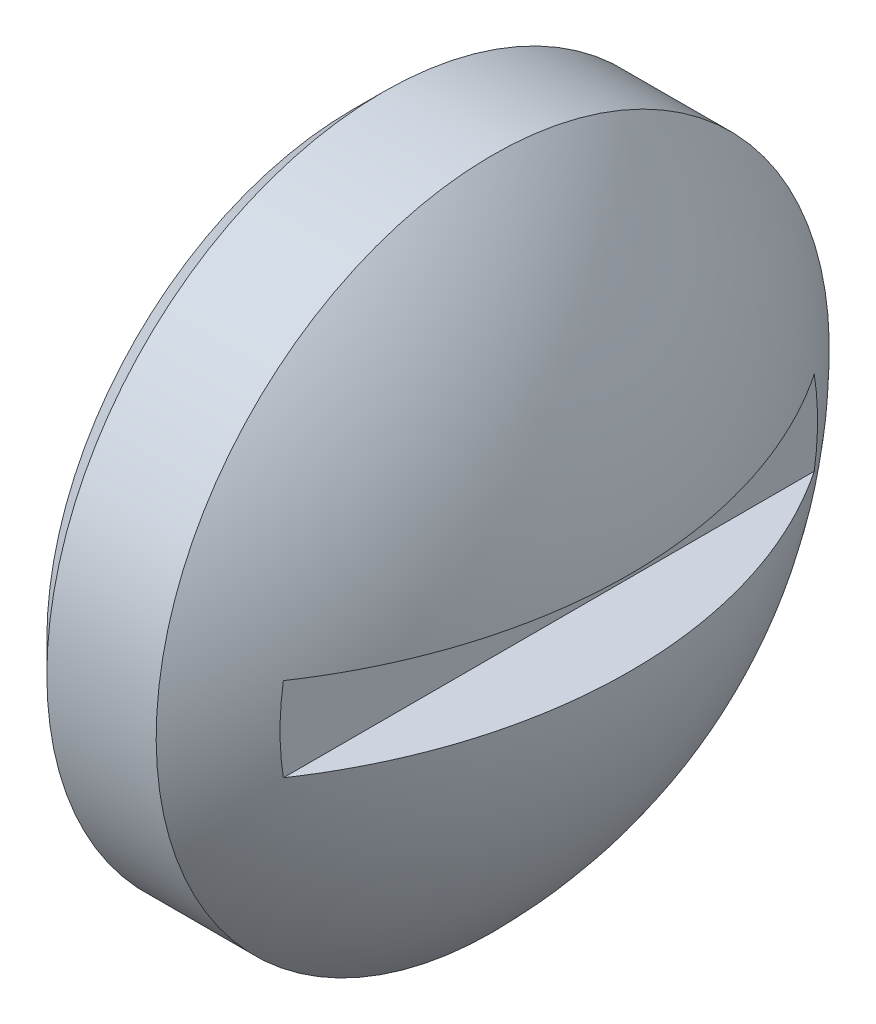
SolidWorks part; units mm, degrees
material "Сталь"
ref_plane "Спереди" through (0, 0, 0) normal (0, 0, 1) x (1, 0, 0)
ref_plane "Сверху" through (0, 0, 0) normal (0, 1, 0) x (1, 0, 0)
ref_plane "Справа" through (0, 0, 0) normal (1, 0, 0) x (0, 0, -1)
sketch "Эскиз1" plane through (0, 0, 0) normal (0, 0, 1) x (1, 0, 0)
  line L0 (0, 0) -> (0, 12) construction
  line L1 (0, 12) -> (5, 12)
  line L2 (0, 0) -> (9.0385, 0) construction
  line L3 (0, 7.5) -> (3.5, 7.5)
  line L4 (3.5, 7.5) -> (3.5, 0)
  line L5 (7, 0) -> (7, 1.5)
  line L6 (7, 1.5) -> (9.8921, 1.5)
  line L7 (0, 7.5) -> (0, 12)
  line L8 (3.5, 0) -> (7, 0)
  arc A0 (5, 12) -> (9.8921, 1.5) centre (-7.0416, 0) cw
  dimension "D3" = 17
  dimension "D1" = 12
  dimension "D2" = 5
  dimension "D4" = 3.5
  dimension "D5" = 7.5
  dimension "D6" = 1.5
  dimension "D7" = 7
revolve "Повернуть1" add sketch "Эскиз1" angle 360 about L2
cosmetic thread "Условное изображение резьбы1" parameters "D1"=5, "D2"=21.797
chamfer "Фаска1" distance 1.1015 angle 45 1 edges at (0, -12, 0)
sketch "Эскиз2" plane through (7, 0, 0) normal (1, 0, 0) x (0, 0, -1)
  line L1 (-25, -1.5) -> (25, -1.5)
  line L2 (-25, -1.5) -> (-25, 1.5)
  line L3 (-25, 1.5) -> (25, 1.5)
  line L4 (25, -1.5) -> (25, 1.5)
  line L5 (-25, -1.5) -> (25, 1.5) construction
  line L6 (-25, 1.5) -> (25, -1.5) construction
  circle A0 centre (0, 0) radius 1.5 construction
  point P0 (0, 0)
  dimension "D1" = 50
extrude "Вырез-Вытянуть1" cut sketch "Эскиз2" along normal through all
